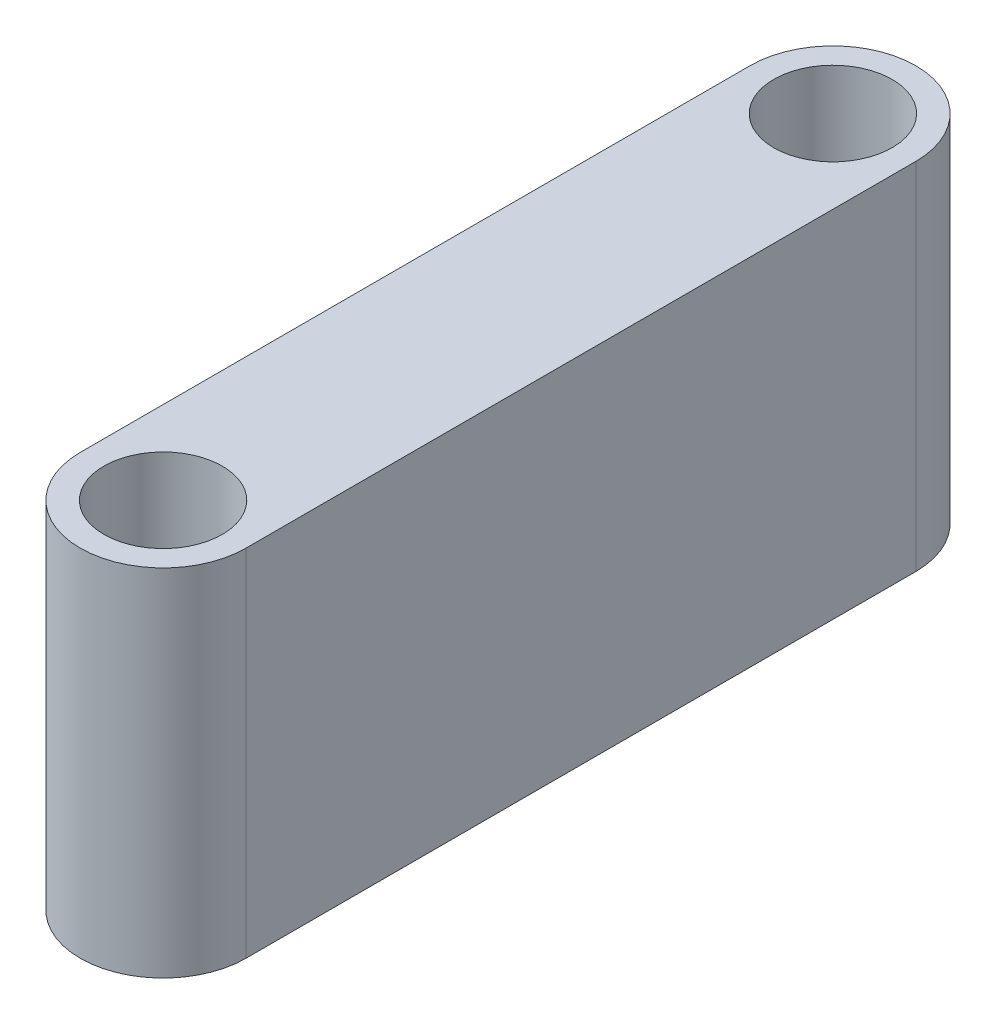
SolidWorks part; units mm, degrees
ref_plane "Front Plane" through (0, 0, 0) normal (0, 0, 1) x (1, 0, 0)
ref_plane "Top Plane" through (0, 0, 0) normal (0, 1, 0) x (1, 0, 0)
ref_plane "Right Plane" through (0, 0, 0) normal (1, 0, 0) x (0, 0, -1)
sketch "Sketch2" plane through (0, 0, 0) normal (0, 1, 0) x (1, 0, 0)
  line L1 (13.5155, 17.9605) -> (13.5155, -17.9605)
  line L2 (-17.9605, -17.9605) -> (17.9605, -17.9605) construction
  line L3 (-17.9605, -17.9605) -> (-17.9605, 17.9605) construction
  line L4 (-17.9605, 17.9605) -> (17.9605, 17.9605) construction
  line L5 (17.9605, -17.9605) -> (17.9605, -14.7855) construction
  line L6 (-17.9605, -17.9605) -> (17.9605, 17.9605) construction
  line L7 (-17.9605, 17.9605) -> (13.5155, -13.5155) construction
  line L8 (22.4055, 17.9605) -> (22.4055, -17.9605)
  line L9 (17.9605, 13.5155) -> (17.9605, 14.7855) construction
  line L10 (17.9605, 14.7855) -> (17.9605, 17.9605) construction
  line L11 (17.9605, -14.7855) -> (17.9605, -13.5155) construction
  line L12 (17.9605, -13.5155) -> (17.9605, 13.5155) construction
  line L13 (13.5155, -13.5155) -> (14.8174, -14.8174) construction
  line L14 (14.8174, -14.8174) -> (17.9605, -17.9605) construction
  circle A1 centre (0, 0) radius 36.5125 construction
  circle A2 centre (17.9605, -17.9605) radius 3.175
  circle A3 centre (17.9605, 17.9605) radius 3.175
  arc A4 (22.4055, 17.9605) -> (13.5155, 17.9605) centre (17.9605, 17.9605) ccw
  arc A5 (13.5155, -17.9605) -> (22.4055, -17.9605) centre (17.9605, -17.9605) ccw
  arc A6 (17.9605, 13.5155) -> (22.4055, 17.9605) centre (17.9605, 17.9605) ccw construction
  arc A7 (14.8174, 14.8174) -> (17.9605, 13.5155) centre (17.9605, 17.9605) ccw construction
  arc A8 (22.4055, -17.9605) -> (17.9605, -13.5155) centre (17.9605, -17.9605) ccw construction
  arc A9 (17.9605, -13.5155) -> (14.8174, -14.8174) centre (17.9605, -17.9605) ccw construction
  arc A10 (14.8174, -14.8174) -> (13.5155, -17.9605) centre (17.9605, -17.9605) ccw construction
  arc A11 (13.5155, 17.9605) -> (14.8174, 14.8174) centre (17.9605, 17.9605) ccw construction
  point P0 (0, 0)
  point P3 (0, 0)
  dimension "D1" = 73.025
  dimension "D3" = 6.35
  dimension "D4" = 6.35
  dimension "D2" = 50.8
  dimension "D5" = 1.27
extrude "Boss-Extrude1" add sketch "Sketch2" along normal mid plane 19.05
sketch "Sketch3" plane through (13.5155, 0, 0) normal (-1, 0, 0) x (0, 0, 1)
  line L1 (-9.97, 6.25) -> (9.97, 6.25) construction
  line L2 (-9.97, 6.25) -> (-9.97, -6.25) construction
  line L3 (-9.97, -6.25) -> (9.97, -6.25) construction
  line L4 (9.97, 6.25) -> (9.97, -6.25) construction
  line L5 (-9.97, 6.25) -> (9.97, -6.25) construction
  line L6 (-9.97, -6.25) -> (9.97, 6.25) construction
  circle A0 centre (-9.97, 6.25) radius 1.95
  circle A1 centre (9.97, 6.25) radius 1.95
  circle A2 centre (9.97, -6.25) radius 1.95
  circle A3 centre (-9.97, -6.25) radius 1.95
  point P0 (0, 0)
  dimension "D3" = 3.9
  dimension "D1" = 19.94
  dimension "D2" = 12.5
extrude "Cut-Extrude1" cut sketch "Sketch3" against normal blind 5.8
equation "\"AIRFRAME_OD\"= 3.142in"
equation "\"AIRFRAME_ID\"= 3.00in"
equation "\"FLAT_T\"= 0.125in"
equation "\"NOSE_EXP_L\"= 3.5in"
equation "\"NOSE_SHOULDER_L\"= 1.5in"
equation "\"MAIN_L\"= 30in"
equation "\"RECO_COUP_L\"= 6in"
equation "\"RECO_SWITCH_L\"= 1.5in"
equation "\"DROGUE_L\"= 14in"
equation "\"ATS_FORE_COUP_L\"= 4in"
equation "\"ATS_AFT_COUP_L\"= 2.5in"
equation "\"LOWER_L\"= 16in"
equation "\"FIN_N\"= 4"
equation "\"CR_AFT_X\"= 0.5in"
equation "\"CR_FORE_X\"= 6in"
equation "\"COUPLER_OD\"= 2.998in"
equation "\"COUPLER_ID\"= 2.875in"
equation "\"RECO_ROD_X\"= 1.5in"
equation "\"ATS_ROD_X\"= 2in"
equation "\"FIN_ROOT\"= 5in"
equation "\"FIN_X\"= 0.75in"
equation "\"MOTOR_OD\"= 2.25in"
equation "\"MOTOR_ID\"= 2.126in"
equation "\"MOTOR_L\"= 8in"
equation "\"MOTOR_LOWER_X\"= 0.5in"
equation "\"NOSE_CONE_L\"=14.5in"
equation "\"ATS_LIPO_L\" = 1.92in"
equation "\"ATS_LIPO_W\" = 0.42in"
equation "\"ATS_LIPO_H\" = 0.94in "
equation "\"ATS_STANDOFF_H\" = 10mm"
equation "\"ATS_STANDOFF_OD\" = 5.2mm"
equation "\"ATS_PCB_L\" = 2.5in"
equation "\"ATS_PCB_W\" = 1.45in"
equation "\"ATS_PCB_H\" = 1.2in"
equation "\"ATS_PCB_HOLESEP_W\" = 1.33in - 0.0985in"
equation "\"ATS_ALTI_L\" = 1.05in"
equation "\"ATS_ALTI_W\" = 0.7in"
equation "\"ATS_ALTI_H\" = 0.4in"
equation "\"D1@Sketch2\"=\"COUPLER_ID\""
